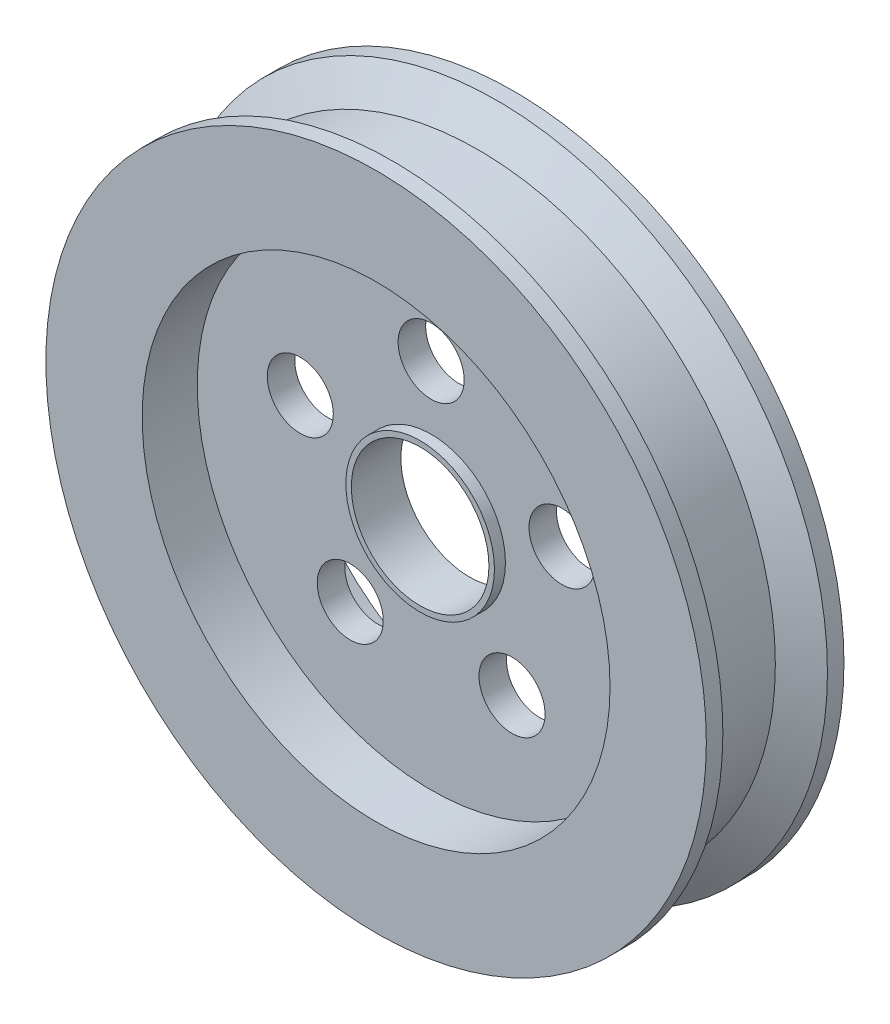
SolidWorks part; units mm, degrees
ref_plane "Front Plane" through (0, 0, 0) normal (0, 0, 1) x (1, 0, 0)
ref_plane "Top Plane" through (0, 0, 0) normal (0, 1, 0) x (1, 0, 0)
ref_plane "Right Plane" through (0, 0, 0) normal (1, 0, 0) x (0, 0, -1)
sketch "Sketch1" plane through (0, 0, 0) normal (0, 0, 1) x (1, 0, 0)
  circle A0 centre (0, 0) radius 12.5
  circle A1 centre (0, 0) radius 60
  dimension "D1" = 25
  dimension "D2" = 120
extrude "Boss-Extrude1" add sketch "Sketch1" along normal mid plane 25
sketch "Sketch2" plane through (0, 0, 12.5) normal (0, 0, 1) x (1, 0, 0)
  circle A0 centre (0, 0) radius 42.5
  dimension "D1" = 85
extrude "Cut-Extrude1" cut sketch "Sketch2" against normal blind 10
mirror "Mirror1" about plane through (0, 0, 0) normal (0, 0, 1) of "Cut-Extrude1"
sketch "Sketch3" plane through (0, 0, 2.5) normal (0, 0, 1) x (1, 0, 0)
  circle A0 centre (0, 25) radius 6
  dimension "D1" = 12
  dimension "D2" = 25
extrude "Cut-Extrude2" cut sketch "Sketch3" against normal through all
pattern_circular "CirPattern1" count 5 over 360 about axis through (0, 0, 0) along (0, 0, 1) of "Cut-Extrude2"
sketch "Sketch4" plane through (0, 0, 0) normal (0, 1, 0) x (1, 0, 0)
  line L0 (60, 9.5) -> (54, 6.0359)
  line L1 (60, -12.5) -> (60, 12.5) construction
  line L2 (54, 6.0359) -> (54, -6.0359)
  line L3 (54, -6.0359) -> (60, -9.5)
  line L4 (60, -9.5) -> (60, 9.5)
  line L5 (0, 0) -> (0, 26.1638) construction
  dimension "D1" = 3
  dimension "D2" = 6
  dimension "D3" = 3
  dimension "D4" = 60
  dimension "D5" = 60
revolve "Cut-Revolve1" cut sketch "Sketch4" angle 360 about L5
sketch "Sketch5" plane through (0, 0, 2.5) normal (0, 0, 1) x (1, 0, 0)
  circle A0 centre (0, 0) radius 13.5
  circle A1 centre (0, 0) radius 12.5 construction
  circle A2 centre (0, 0) radius 12.5
  dimension "D1" = 27
extrude "Boss-Extrude2" add sketch "Sketch5" along normal blind 2 and the other way blind 7
